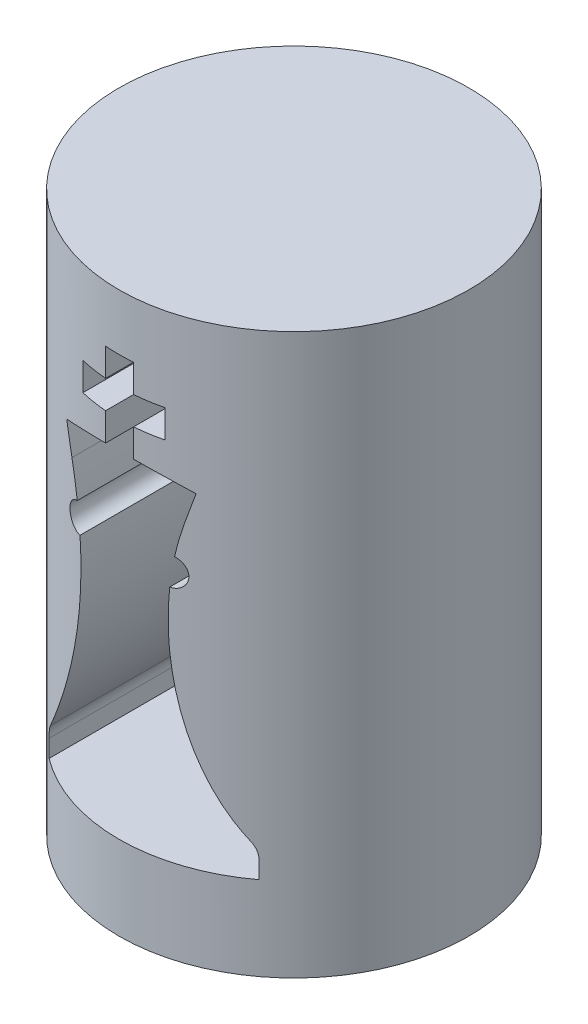
SolidWorks part; units mm, degrees
ref_plane "Front" through (0, 0, 0) normal (0, 0, 1) x (1, 0, 0)
ref_plane "Top" through (0, 0, 0) normal (0, 1, 0) x (1, 0, 0)
ref_plane "Right" through (0, 0, 0) normal (1, 0, 0) x (0, 0, -1)
sketch "Sketch2" plane through (0, 0, 0) normal (0, 1, 0) x (1, 0, 0)
  circle A0 centre (0, 0) radius 12.5
  dimension "D1" = 25
extrude "Boss-Extrude1" add sketch "Sketch2" along normal mid plane 40
sketch "Sketch3" plane through (0, 0, 0) normal (0, 0, 1) x (1, 0, 0)
  line L0 (-7.5, -14) -> (7.5, -14)
  line L2 (-7.5, -12.75) -> (-7.5, -14)
  line L18 (-4.0295, 7.2676) -> (-4.6222, 9.2507)
  line L19 (0, -50) -> (0, 50) construction
  line L20 (4.0295, 7.2676) -> (4.6222, 9.2507)
  line L21 (7.5, -12.75) -> (7.5, -14)
  line L22 (-1, 10) -> (-1, 12)
  line L23 (-1, 12) -> (-2.9263, 12)
  line L24 (-2.9263, 12) -> (-2.9263, 14)
  line L25 (-2.9263, 14) -> (-1, 14)
  line L26 (-1, 14) -> (-1, 16)
  line L27 (-1, 16) -> (1, 16)
  line L28 (1, 16) -> (1, 14)
  line L29 (1, 14) -> (2.9263, 14)
  line L30 (2.9263, 14) -> (2.9263, 12)
  line L31 (2.9263, 12) -> (1, 12)
  line L32 (1, 12) -> (1, 10)
  line L33 (-1, 10) -> (1, 10) construction
  arc A4 (-7.1574, -11.6761) -> (-7.5, -12.75) centre (-5.6457, -12.75) ccw
  arc A30 (-7.1574, -11.6761) -> (-3.2046, 3.001) centre (-25, 1) ccw
  arc A35 (7.1574, -11.6761) -> (7.5, -12.75) centre (5.6457, -12.75) cw
  arc A39 (-4.6222, 9.2507) -> (-1, 10) centre (0, -3.9642) cw
  arc A40 (1, 10) -> (4.6222, 9.2507) centre (0, -3.9642) cw
  arc A41 (-3.4767, 4.974) -> (-3.2046, 3.001) centre (-3.25, 4) ccw
  arc A42 (-3.4767, 4.974) -> (-4.0295, 7.2676) centre (-25, 1) ccw
  arc A43 (3.4767, 4.974) -> (4.0295, 7.2676) centre (25, 1) cw
  arc A44 (3.4767, 4.974) -> (3.2046, 3.001) centre (3.25, 4) cw
  arc A45 (7.1574, -11.6761) -> (3.2046, 3.001) centre (25, 1) cw
  point P0 (0, -14)
  point P24 (0, 10)
  point P26 (0, 16)
  point P27 (2.9263, 13)
  point P28 (-2.9263, 13)
  dimension "D1" = 2
  dimension "D6" = 1.25
  dimension "D7" = 1
  dimension "D9" = 25
  dimension "D5" = 2
  dimension "D4" = 30
  dimension "D10" = 14
  dimension "D11" = 6.5
  dimension "D2" = 15
  dimension "D3" = 14
  dimension "D8" = 1
  dimension "D12" = 4
extrude "Cut-Extrude1" cut sketch "Sketch3" against normal through all both and the other way through all
sketch "Sketch4" plane through (0, -20, 0) normal (0, -1, 0) x (-1, 0, 0)
  circle A0 centre (0, 0) radius 3
  dimension "D1" = 6
extrude "Cut-Extrude2" cut sketch "Sketch4" against normal blind 3
